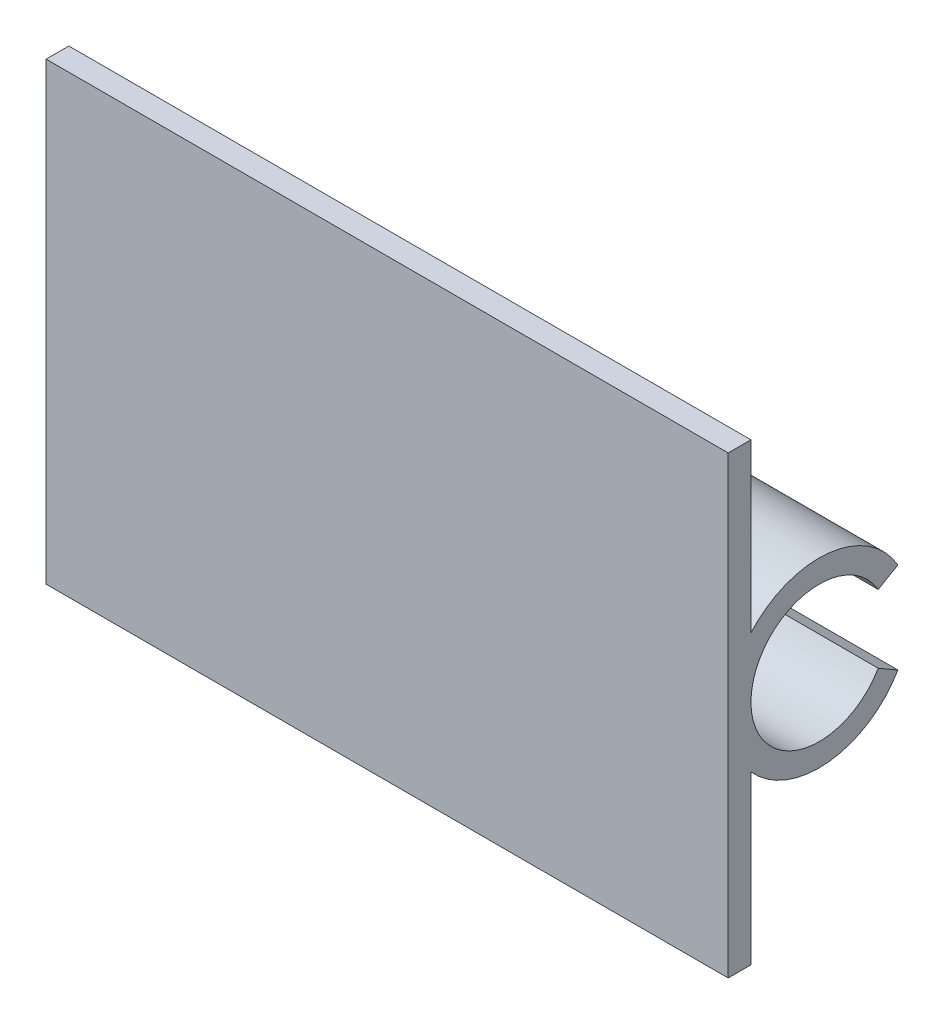
SolidWorks part; units mm, degrees
material "eSUN ePLA-LW"
ref_plane "Front Plane" through (0, 0, 0) normal (0, 0, 1) x (1, 0, 0)
ref_plane "Top Plane" through (0, 0, 0) normal (0, 1, 0) x (1, 0, 0)
ref_plane "Right Plane" through (0, 0, 0) normal (1, 0, 0) x (0, 0, -1)
sketch "Sketch2" plane through (0, 0, 0) normal (1, 0, 0) x (0, 0, -1)
  arc A0 (0, 0) -> (6.7177, 1.8) centre (3.6, 0) cw
  point P5 (-2.2956, 0)
  point P6 (-1.3307, 2.0885)
  point P7 (5.6037, 0.3088)
  point P8 (0, 0)
  dimension "D2" = 3.6
  dimension "D1" = 150
sketch "Sketch11" plane through (0, 0, 0) normal (0, 0, 1) x (1, 0, 0)
  line L0 (0, 0) -> (36, 0)
  line L1 (0, 0) -> (0, 12)
  line L5 (0, 12) -> (36, 12)
  line L6 (36, 12) -> (36, 0)
  line L7 (36, 0) -> (90.211, 0) construction
  point P3 (0, 1.5812)
  point P5 (43, 12)
  point P6 (0, 12)
  point P10 (0, 1.9722)
  point P11 (6.0558, 6)
  point P13 (0, 4.067)
  point P14 (0, 6)
  point P15 (0.6343, 6)
  point P16 (0.6343, 12)
  dimension "D1" = 24
  dimension "D4" = 36
extrude "Boss-Extrude3" add sketch "Sketch11" along normal blind 1.2 contours L5 L6 L0 L1
extrude "Extrude-Thin2" add sketch "Sketch2" against normal blind 10 from surface at 36 thin starting at face at (36, 6, 0.6) thin type one direction reverse wall 1.2
mirror "Mirror1" about plane through (0, 0, 0) normal (0, 1, 0) of bodies 109
